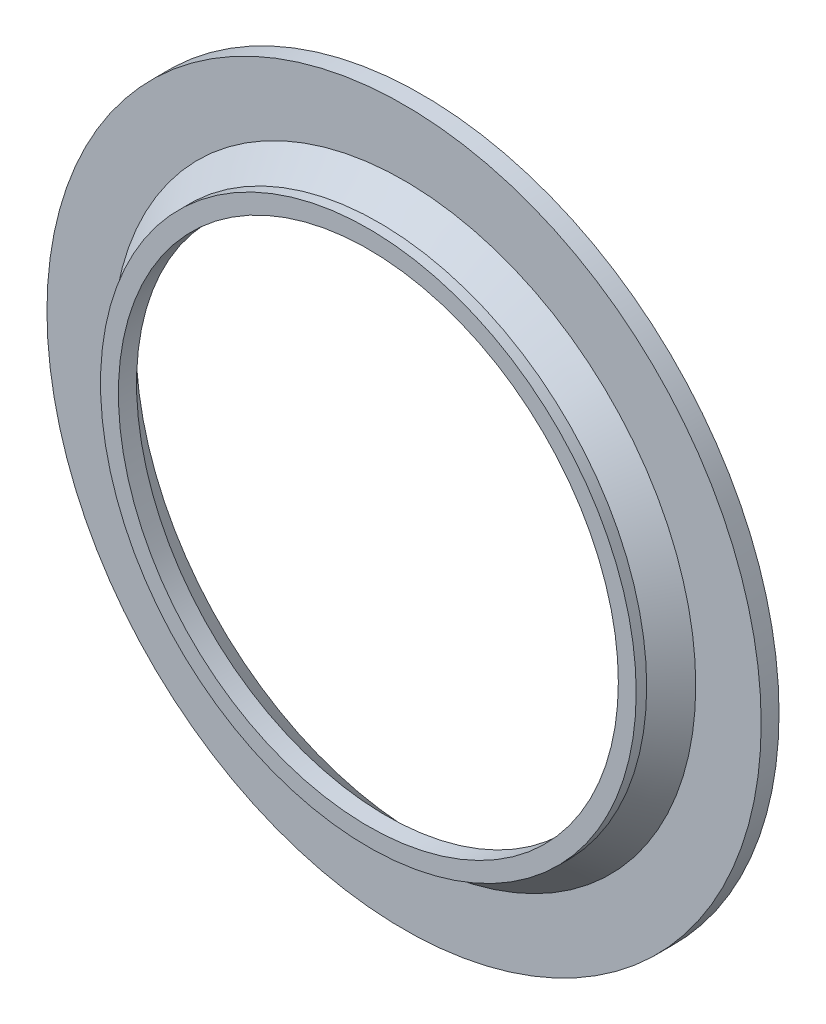
SolidWorks part; units mm, degrees
ref_plane "Front Plane" through (0, 0, 0) normal (0, 0, 1) x (1, 0, 0)
ref_plane "Top Plane" through (0, 0, 0) normal (0, 1, 0) x (1, 0, 0)
ref_plane "Right Plane" through (0, 0, 0) normal (1, 0, 0) x (0, 0, -1)
sketch "Sketch1" plane through (0, 0, 0) normal (0, 1, 0) x (1, 0, 0)
  line L0 (1.5, 0) -> (1.5, 0.0588)
  line L1 (1.5, 0.0588) -> (1.6335, 0.2)
  line L2 (1.6335, 0.2) -> (2, 0.2)
  line L3 (1.5, 0) -> (1.4, 0)
  line L4 (1.4, 0) -> (1.4, 0.1017)
  line L5 (1.4, 0.1017) -> (1.602, 0.3)
  line L6 (1.602, 0.3) -> (2, 0.3)
  line L7 (2, 0.3) -> (2, 0.2)
  line L8 (0, 0) -> (0, 1.1414) construction
  dimension "D1" = 1.5
  dimension "D2" = 0.3
  dimension "D3" = 0.1
  dimension "D4" = 2
  dimension "D5" = 0.1
revolve "Revolve1" add sketch "Sketch1" angle 360 about L8
